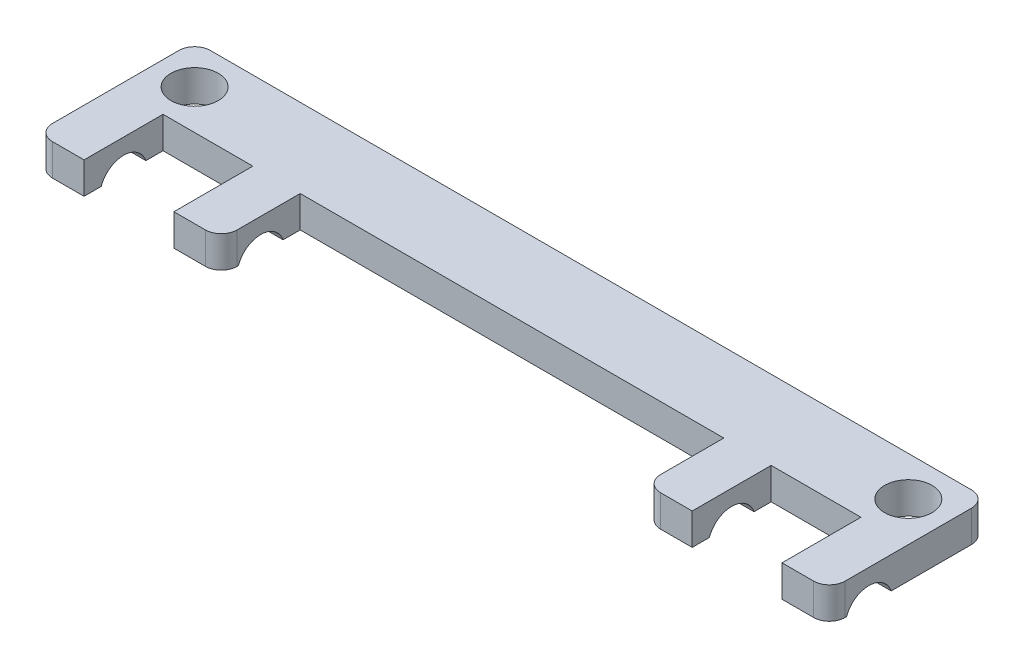
SolidWorks part; units mm, degrees
ref_plane "Front Plane" through (0, 0, 0) normal (0, 0, 1) x (1, 0, 0)
ref_plane "Top Plane" through (0, 0, 0) normal (0, 1, 0) x (1, 0, 0)
ref_plane "Right Plane" through (0, 0, 0) normal (1, 0, 0) x (0, 0, -1)
sketch "Sketch1" plane through (0, 0, 0) normal (0, 1, 0) x (1, 0, 0)
  line L0 (25.1, 5) -> (25.1, 0) construction
  line L1 (0, 0) -> (50.2, 0)
  line L2 (0, 0) -> (0, 5)
  line L3 (0, 5) -> (50.2, 5)
  line L4 (50.2, 0) -> (50.2, 5)
  line L5 (0, 0) -> (3, 0)
  line L6 (0, 0) -> (0, -5)
  line L7 (0, -5) -> (3, -5)
  line L8 (3, 0) -> (3, -5)
  line L9 (41.5127, -5) -> (38.5127, -5)
  line L10 (8.6873, 0) -> (11.6873, 0)
  line L11 (8.6873, 0) -> (8.6873, -5)
  line L12 (8.6873, -5) -> (11.6873, -5)
  line L13 (11.6873, 0) -> (11.6873, -5)
  line L14 (38.5127, 0) -> (38.5127, -5)
  line L15 (41.5127, 0) -> (38.5127, 0)
  line L16 (41.5127, 0) -> (41.5127, -5)
  line L17 (50.2, -5) -> (47.2, -5)
  line L18 (47.2, 0) -> (47.2, -5)
  line L19 (50.2, 0) -> (47.2, 0)
  line L20 (50.2, 0) -> (50.2, -5)
  circle A0 centre (2.5, 2.5) radius 1.5
  circle A1 centre (47.7, 2.5) radius 1.5
  dimension "D2" = 3
  dimension "D3" = 3
  dimension "D5" = 2.5
  dimension "D6" = 2.5
  dimension "D7" = 45.2
  dimension "D8" = 2.5
  dimension "D1" = 2.5
  dimension "D4" = 5
  dimension "D9" = 3
  dimension "D10" = 5
extrude "Boss-Extrude1" add sketch "Sketch1" along normal blind 2 contours L3 L0 L1 L4 A1 | L0 L3 L2 L1 A0 | L13 L1 L11 L12 | L8 L1 L6 L7 | L16 L1 L14 L9 | L20 L1 L18 L17
sketch "Sketch2" plane through (0, 0, 0) normal (-1, 0, 0) x (0, 0, 1)
  line L0 (0, 2) -> (0, 0) construction
  line L1 (0, 2) -> (0, 0)
  line L4 (-5, 0) -> (5, 0)
  line L5 (5, 0) -> (5, 2)
  line L6 (5, 2) -> (-5, 2)
  line L7 (-5, 2) -> (-5, 0)
  line L8 (-5, 0) -> (5, 0)
  line L9 (5, 0) -> (5, 2)
  line L10 (5, 2) -> (-5, 2)
  line L11 (-5, 2) -> (-5, 0)
  circle A0 centre (2.5, -0.5) radius 1.5
  dimension "D2" = 3
  dimension "D3" = 2.5
  dimension "D4" = 2.5
  dimension "D1" = 0
extrude "Cut-Extrude1" cut sketch "Sketch2" against normal blind 55 contours A0
fillet "Fillet1" radius 1 6 edges at (0, 1, -5) (50.2, 1, -5) (50.2, 1, 5) (38.5127, 1, 5) (11.6873, 1, 5) (0, 1, 5)
